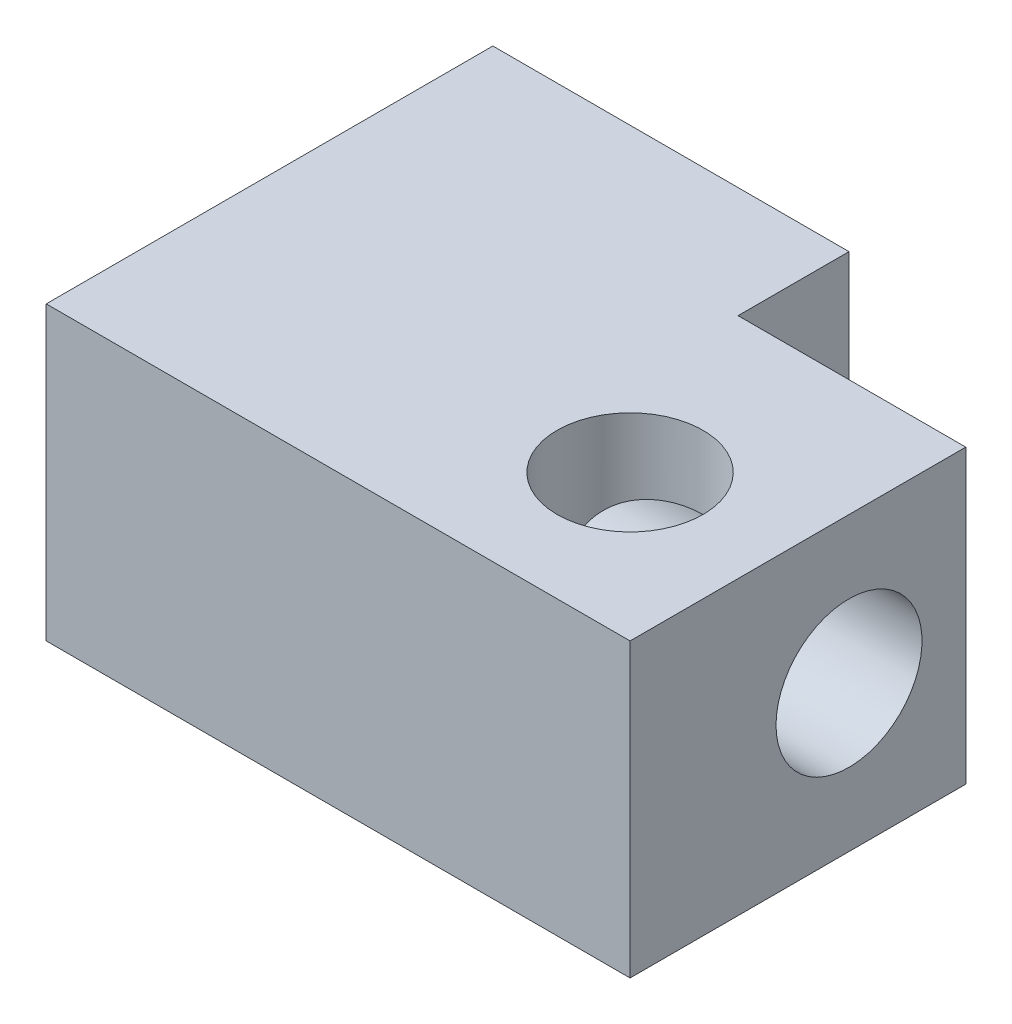
SolidWorks part; units mm, degrees
ref_plane "Front Plane" through (0, 0, 0) normal (0, 0, 1) x (1, 0, 0)
ref_plane "Top Plane" through (0, 0, 0) normal (0, 1, 0) x (1, 0, 0)
ref_plane "Right Plane" through (0, 0, 0) normal (1, 0, 0) x (0, 0, -1)
sketch "Sketch4" plane through (0, 0, 0) normal (0, 1, 0) x (1, 0, 0)
  line L5 (5, -86) -> (79, -86)
  line L9 (5, -7.5) -> (5, -86) construction
  line L11 (91.25, -2.5) -> (91.25, -88.5)
  line L12 (79, -5) -> (79, -7.5)
  line L13 (79, -83.5) -> (82.9, -83.5)
  line L14 (82.9, -82.1) -> (82.9, -83.5)
  line L15 (5, -83.5) -> (81.5, -83.5) construction
  line L16 (79, -88.5) -> (91.25, -88.5)
  line L17 (82.9, -82.1) -> (91.25, -82.1)
  line L18 (-4.75, -45.5) -> (91.25, -45.5)
  line L19 (79, -82.1) -> (91.25, -82.1) construction
  line L20 (79, -83.5) -> (79, -88.5)
  line L21 (79, -2.5) -> (91.25, -2.5)
  line L22 (79, -7.5) -> (79, -2.5)
  line L23 (79, -83.5) -> (91.25, -83.5) construction
  line L24 (79, -7.5) -> (82.9, -7.5)
  line L25 (5, -86) -> (81.5, -86) construction
  line L26 (82.9, -8.9) -> (91.25, -8.9)
  line L27 (82.9, -8.9) -> (82.9, -7.5)
  line L28 (43.25, -45.5) -> (43.25, -57.8047)
  line L29 (3.6, -8.9) -> (-2.5, -8.9)
  line L30 (3.6, -8.9) -> (3.6, -7.5)
  line L31 (7.5, -7.5) -> (3.6, -7.5)
  line L32 (7.5, -7.5) -> (7.5, -2.5)
  line L33 (7.5, -2.5) -> (-2.5, -2.5)
  line L34 (7.5, -5) -> (79, -5)
  line L35 (-4.75, -45.5) -> (-4.75, -86)
  line L36 (5, -7.5) -> (5, -86)
  line L37 (7.5, -5) -> (79, -5) construction
  line L38 (-2.5, -2.5) -> (-2.5, -8.9)
  line L39 (7.5, -82.75) -> (7.5, -88.5)
  line L40 (3.6, -80.85) -> (3.6, -82.75)
  line L43 (7.5, -88.5) -> (-2.5, -88.5)
  line L44 (-2.5, -88.5) -> (-2.5, -80.85)
  line L45 (3.6, -80.85) -> (-2.5, -80.85)
  line L47 (7.5, -82.75) -> (3.6, -82.75)
  circle A0 centre (5, -5) radius 1.25
  circle A1 centre (81.5, -5) radius 1.25
  circle A2 centre (81.5, -86) radius 1.25
  circle A3 centre (5, -86) radius 1.25
  point P1 (7.5, -83.5)
  point P4 (82.9, -5)
  point P7 (81.5, -86)
  point P8 (81.5, -5)
  point P27 (82.9, -86)
  point P48 (3.6, -83.5)
  point P53 (7.5, -82.25)
  point P54 (3.6, -82.25)
  dimension "D1" = 2
  dimension "D2" = 2
extrude "Boss-Extrude1" add sketch "Sketch4" along normal blind 5
sketch "Sketch5" plane through (-2.5, 0, 0) normal (-1, 0, 0) x (0, 0, 1)
  line L0 (88.5, 0) -> (88.5, 5)
  line L1 (84.75, 0) -> (84.75, 5)
  circle A0 centre (84.75, 2.5) radius 1.25
  dimension "D1" = 3.75
extrude "Cut-Extrude1" cut sketch "Sketch5" against normal blind 10 contours L1 A0 | L1 A0
